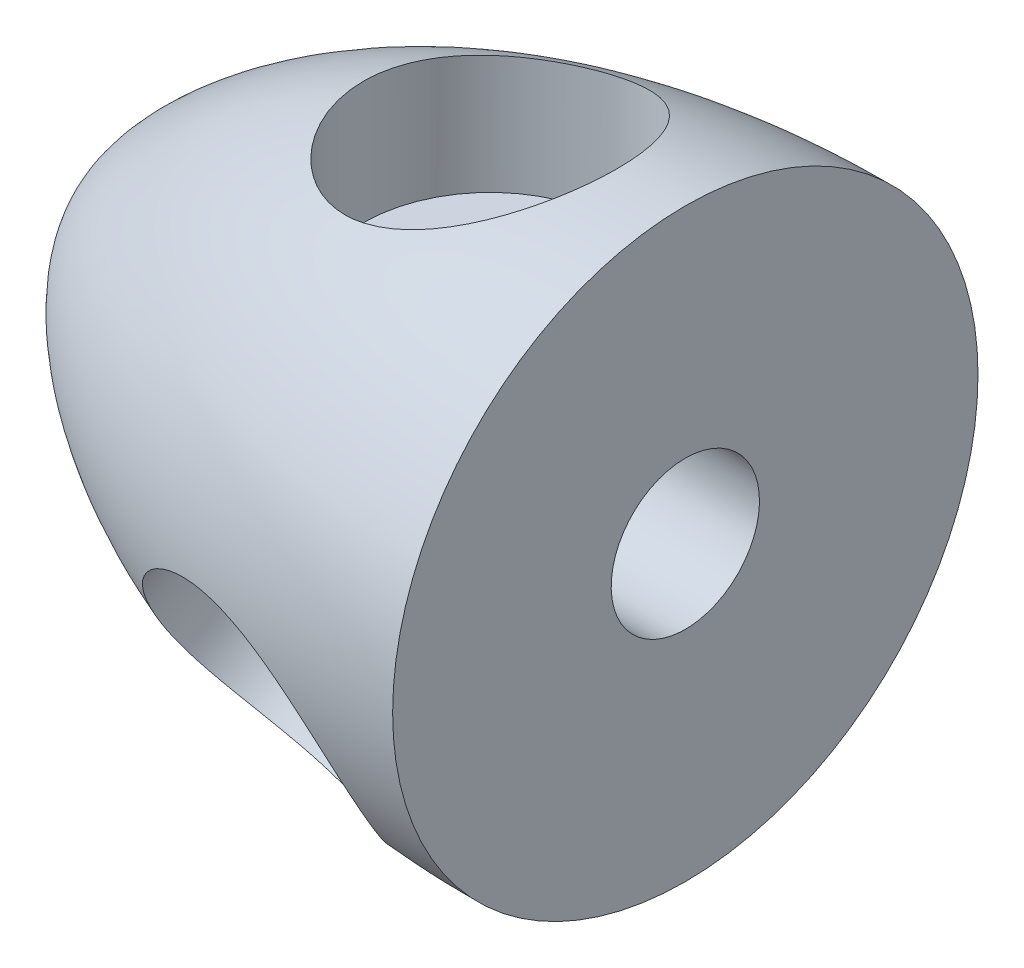
SolidWorks part; units mm, degrees
ref_plane "Front Plane" through (0, 0, 0) normal (0, 0, 1) x (1, 0, 0)
ref_plane "Top Plane" through (0, 0, 0) normal (0, 1, 0) x (1, 0, 0)
ref_plane "Right Plane" through (0, 0, 0) normal (1, 0, 0) x (0, 0, -1)
sketch "Sketch1" plane through (0, 0, 0) normal (0, 0, 1) x (1, 0, 0)
  line L0 (0, 19.05) -> (0, 0)
  line L1 (0, 0) -> (-38.1, 0)
  line L2 (-6.7617, 19.05) -> (6.7617, 19.05) construction
  line L3 (-38.1, -5.0533) -> (-38.1, 5.0533) construction
  spline S0 degree 3 poles (0, 19.05) (-25.41, 19.05) (-38.1, 6.3167) (-38.1, 0) knots 0 0 0 0 1 1 1 1
  dimension "D1" = 18.95
  dimension "D2" = 76.23
  dimension "D3" = 38.1
  dimension "D4" = 19.05
revolve "Revolve1" add sketch "Sketch1" angle 360 about L1
ref_plane "Plane1" through (0, 19.05, 0) normal (0, 1, 0) x (1, 0, 0)
sketch "Sketch2" plane through (0, 19.05, 0) normal (0, 1, 0) x (1, 0, 0)
  line L0 (-12.7, 0) -> (0, 0) construction
  circle A0 centre (-12.7, 0) radius 8.255
  dimension "D2" = 16.51
  dimension "D1" = 12.7
extrude "Cut-Extrude1" cut sketch "Sketch2" against normal blind 11.43
pattern_circular "CirPattern1" count 3 over 360 about axis through (0, 0, 0) along (1, 0, 0) of "Cut-Extrude1"
sketch "Sketch3" plane through (0, 0, 0) normal (1, 0, 0) x (0, 0, -1)
  circle A0 centre (0, 0) radius 4.826
  dimension "D1" = 9.652
extrude "Cut-Extrude2" cut sketch "Sketch3" against normal blind 12.7
